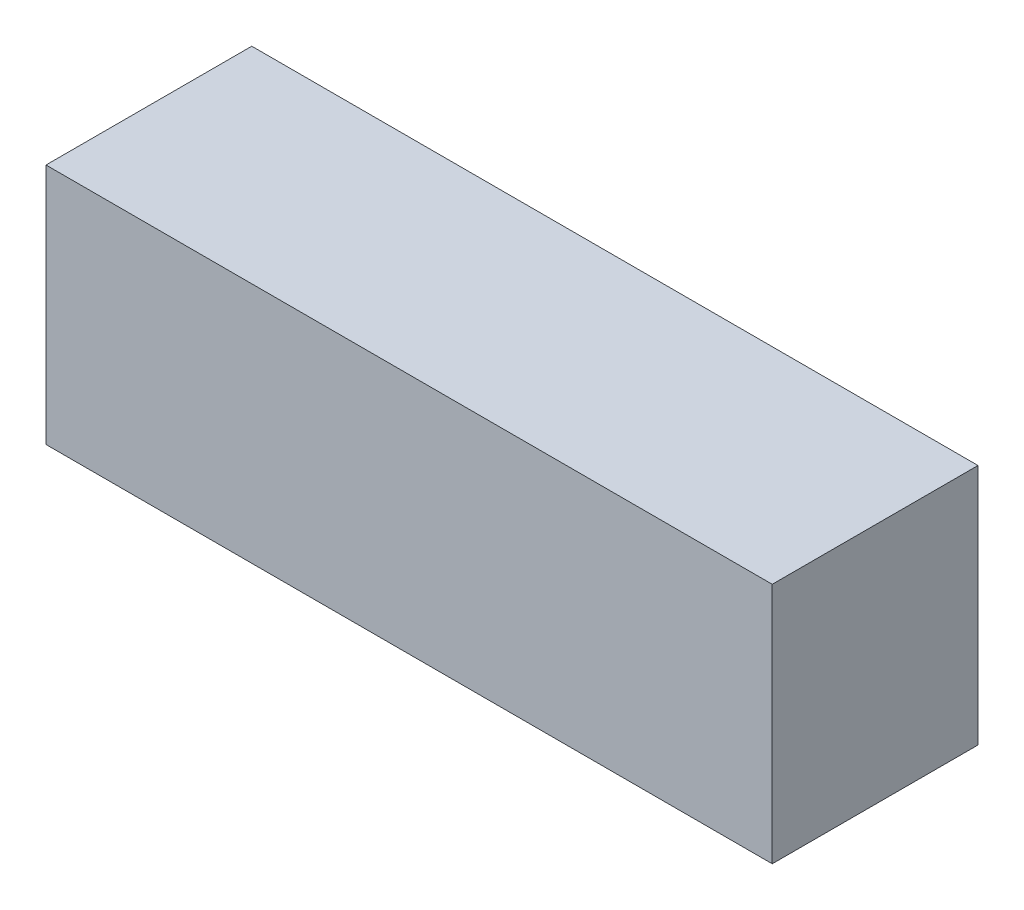
SolidWorks part; units mm, degrees
ref_plane "Front Plane" through (0, 0, 0) normal (0, 0, 1) x (1, 0, 0)
ref_plane "Top Plane" through (0, 0, 0) normal (0, 1, 0) x (1, 0, 0)
ref_plane "Right Plane" through (0, 0, 0) normal (1, 0, 0) x (0, 0, -1)
sketch "Sketch1" plane through (0, 0, 0) normal (0, 1, 0) x (1, 0, 0)
  line L1 (-30, 8.5) -> (30, 8.5)
  line L2 (-30, 8.5) -> (-30, -8.5)
  line L3 (-30, -8.5) -> (30, -8.5)
  line L4 (30, 8.5) -> (30, -8.5)
  line L5 (-30, 8.5) -> (30, -8.5) construction
  line L6 (-30, -8.5) -> (30, 8.5) construction
  point P0 (0, 0)
  dimension "D1" = 17
  dimension "D2" = 60
extrude "Boss-Extrude1" add sketch "Sketch1" along normal blind 20
